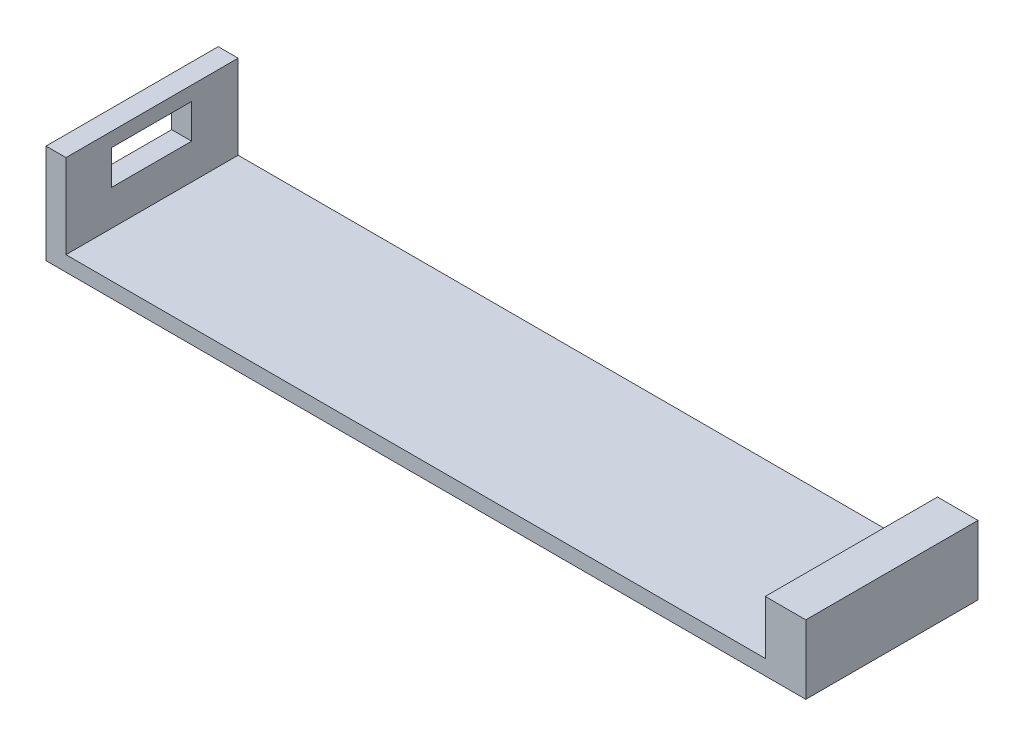
SolidWorks part; units mm, degrees
ref_plane "Front Plane" through (0, 0, 0) normal (0, 0, 1) x (1, 0, 0)
ref_plane "Top Plane" through (0, 0, 0) normal (0, 1, 0) x (1, 0, 0)
ref_plane "Right Plane" through (0, 0, 0) normal (1, 0, 0) x (0, 0, -1)
sketch "Sketch1" plane through (0, 0, 0) normal (0, 1, 0) x (1, 0, 0)
  line L1 (-41.0507, 0.5131) -> (33.9493, 0.5131)
  line L2 (-41.0507, 0.5131) -> (-41.0507, -16.4869)
  line L3 (-41.0507, -16.4869) -> (33.9493, -16.4869)
  line L4 (33.9493, 0.5131) -> (33.9493, -16.4869)
  dimension "D1" = 75
  dimension "D2" = 17
extrude "Boss-Extrude1" add sketch "Sketch1" along normal blind 1.5
sketch "Sketch2" plane through (0, 1.5, 0) normal (0, 1, 0) x (1, 0, 0)
  line L0 (-41.0507, -16.4869) -> (33.9493, -16.4869) construction
  line L2 (33.9493, 0.5131) -> (-41.0507, 0.5131) construction
  line L3 (29.9493, 0.5131) -> (29.9493, -16.4869)
  line L4 (29.9493, -16.4869) -> (33.9493, -16.4869)
  line L5 (33.9493, -16.4869) -> (33.9493, 0.5131)
  line L6 (33.9493, 0.5131) -> (29.9493, 0.5131)
  line L7 (-41.0507, 0.5131) -> (-41.0507, -16.4869) construction
  line L8 (-41.0507, 0.5131) -> (-41.0507, -16.4869)
  line L9 (-41.0507, 0.5131) -> (-39.0814, 0.5131)
  line L10 (-41.0507, -16.4869) -> (-39.0814, -16.4869)
  line L11 (-39.0814, 0.5131) -> (-39.0814, -16.4869)
  point P0 (33.9493, -16.4869)
  point P7 (-39.0507, -16.4869)
  point P9 (33.9493, 0.5131)
  point P10 (29.9493, 0.5131)
  point P12 (29.9493, -16.4869)
  point P18 (-41.0507, -7.9869)
  point P19 (-41.0507, -7.9869)
  dimension "D1" = 4
  dimension "D2" = 4
  dimension "D3" = 69
  dimension "D4" = 2
extrude "Boss-Extrude2" add sketch "Sketch2" along normal blind 5.3
sketch "Sketch3" plane through (29.9493, 0, 0) normal (-1, 0, 0) x (0, 0, 1)
  line L0 (-0.5131, 1.5) -> (16.4869, 1.5) construction
  line L1 (0.9869, 4.8) -> (0.9869, 3.5)
  line L2 (0.9869, 4.8) -> (15.0429, 4.8)
  line L3 (0.9869, 3.5) -> (15.0429, 3.5)
  line L4 (15.0429, 4.8) -> (15.0429, 3.5)
  point P0 (0.9869, 1.5)
  point P1 (14.9869, 1.5)
  point P4 (7.9869, 1.5)
  point P5 (7.9869, 1.5)
  point P6 (0.9869, 3.5)
  point P7 (14.9869, 3.5)
  point P8 (0.9869, 4.8)
  point P9 (14.9869, 4.8)
  dimension "D1" = 7
  dimension "D2" = 7
  dimension "D3" = 2
  dimension "D4" = 2
  dimension "D5" = 1.3
  dimension "D6" = 1.3
extrude "Cut-Extrude1" cut sketch "Sketch3" against normal blind 2.1
sketch "Sketch4" plane through (0, 6.8, 0) normal (0, 1, 0) x (1, 0, 0)
  line L1 (-41.0507, 0.5131) -> (-39.0814, 0.5131)
  line L2 (-41.0507, 0.5131) -> (-41.0507, -16.4869)
  line L3 (-41.0507, -16.4869) -> (-39.0814, -16.4869)
  line L4 (-39.0814, 0.5131) -> (-39.0814, -16.4869)
extrude "Boss-Extrude3" add sketch "Sketch4" along normal blind 3
sketch "Sketch5" plane through (-39.0814, 0, 0) normal (1, 0, 0) x (0, 0, -1)
  line L0 (-16.4869, 1.5) -> (0.5131, 1.5) construction
  line L2 (-11.9869, 8.4) -> (-11.9869, 5)
  line L3 (-11.9869, 8.4) -> (-4.0808, 8.4)
  line L4 (-11.9869, 5) -> (-4.0808, 5)
  line L5 (-4.0808, 8.4) -> (-4.0808, 5)
  point P0 (-3.9869, 1.5)
  point P1 (-11.9869, 1.5)
  point P4 (-7.9869, 1.5)
  point P5 (-7.9869, 1.5)
  point P6 (-3.9869, 5)
  point P7 (-11.9869, 5)
  point P8 (-11.9869, 8.4)
  point P9 (-3.9869, 8.4)
  dimension "D1" = 4
  dimension "D2" = 4
  dimension "D3" = 3.5
  dimension "D4" = 3.5
  dimension "D5" = 3.4
  dimension "D6" = 3.4
extrude "Cut-Extrude3" cut sketch "Sketch5" against normal blind 33
